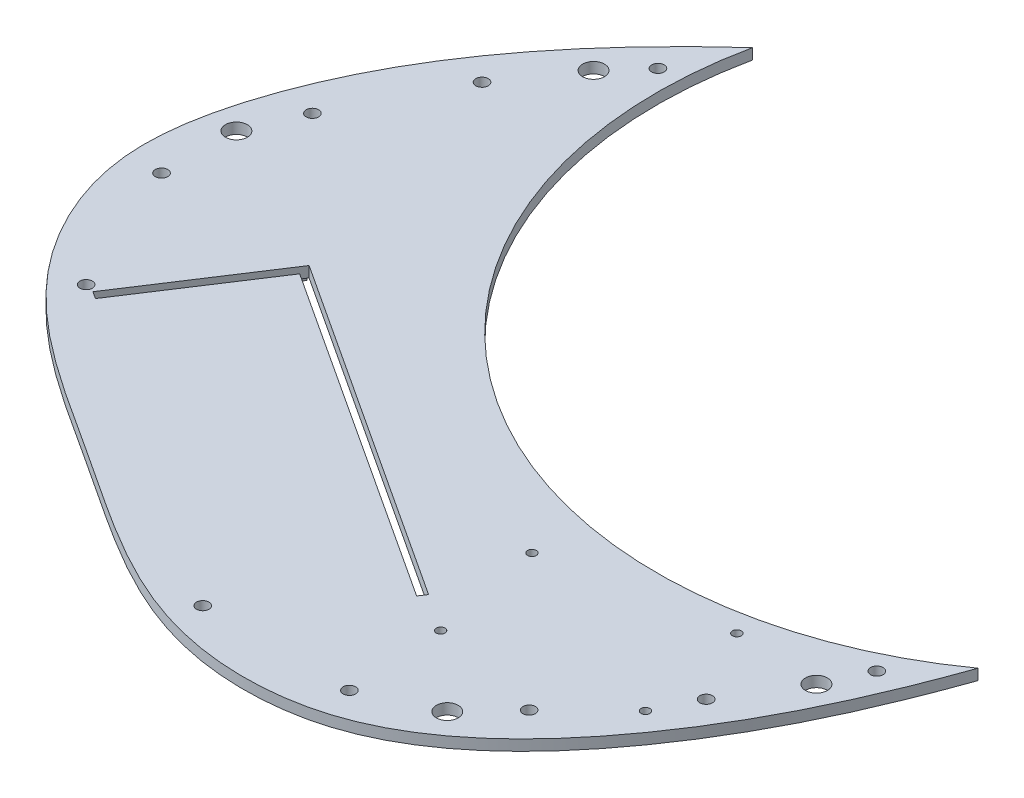
SolidWorks part; units mm, degrees
ref_plane "Front Plane" through (0, 0, 0) normal (0, 0, 1) x (1, 0, 0)
ref_plane "Top Plane" through (0, 0, 0) normal (0, 1, 0) x (1, 0, 0)
ref_plane "Right Plane" through (0, 0, 0) normal (1, 0, 0) x (0, 0, -1)
sketch "Sketch1" plane through (0, 0, 0) normal (0, 1, 0) x (1, 0, 0)
  line L0 (0, 0) -> (0, 58.1546) construction
  circle A0 centre (0, 29.0773) radius 4.9726
extrude "Boss-Extrude1" add sketch "Sketch1" along normal blind 2.5
sketch "Sketch3" plane through (0, 2.5, 0) normal (0, 1, 0) x (1, 0, 0)
  point P0 (0, 29.0773)
sketch "Sketch4" plane through (0, 2.5, 0) normal (0, 1, 0) x (1, 0, 0)
  arc A0 (127.8362, 60.0219) -> (-23.0143, 158.5764) centre (71.5138, 138.5385) cw
  spline S0 degree 3 poles (-23.0143, 158.5764) (-43.5254, 139.9346) (-67.442, 110.6065) (-77.0529, 62.2895) (-62.2823, 29.9156) (-37.7055, 11.9817) (-7.3418, -7.1852) (21.5414, -27.9257) (71.8699, -27.6215) (107.5055, 10.8983) (121.7705, 42.9102) (127.8362, 60.0219) knots 0 0 0 0 0.208615 0.280864 0.361665 0.463001 0.507838 0.636521 0.725182 0.864473 1 1 1 1
  spline S1 degree 3 poles (127.8362, 60.0219) (117.8116, 31.8423) (99.3254, -5.8403) (50.0509, -31.8426) (12.7306, -21.8834) (-18.6736, 0.4949) (-51.7822, 20.2645) (-75.8943, 50.4406) (-71.8759, 106.0099) (-44.7933, 138.0763) (-23.0143, 158.5764) knots 0.001048 0.001048 0.001048 0.001048 0.232378 0.297499 0.407563 0.5 0.592437 0.702501 0.767622 0.998952 0.998952 0.998952 0.998952 construction
extrude "Boss-Extrude2" add sketch "Sketch4" against normal blind 2.5
sketch "Sketch5" plane through (0, 0, 0) normal (0, -1, 0) x (-1, 0, 0)
  line L0 (-100.0794, 11.3416) -> (-94.3668, 41.2815)
  line L1 (-100.0794, 11.3416) -> (-56.4171, 3.0108)
  line L2 (-94.3668, 41.2815) -> (-50.7045, 32.9506)
  line L3 (-56.4171, 3.0108) -> (-50.7045, 32.9506)
  line L4 (-97.2231, 26.3116) -> (-53.5608, 17.9807) construction
  line L5 (-72.5356, 37.1161) -> (-78.2482, 7.1762) construction
  line L6 (-53.5608, 17.9807) -> (-27.1139, 12.9346) construction
  line L7 (-28.3016, 6.7096) -> (-54.7485, 11.7557)
  line L8 (-28.3016, 6.7096) -> (-25.9261, 19.1596)
  line L9 (-54.7485, 11.7557) -> (-52.373, 24.2057)
  line L10 (-25.9261, 19.1596) -> (-52.373, 24.2057)
  line L11 (-28.3016, 6.7096) -> (-52.373, 24.2057) construction
  line L12 (-54.7485, 11.7557) -> (-25.9261, 19.1596) construction
  circle A0 centre (-92.8526, 39.0532) radius 1.016
  circle A1 centre (-97.8511, 12.8558) radius 1.016
  circle A2 centre (-52.9327, 31.4364) radius 1.016
  circle A3 centre (-57.9313, 5.239) radius 1.016
  point P12 (-40.3373, 15.4576)
  point P19 (-40.3373, 15.4576)
  dimension "D3" = 2.032
  dimension "D1" = 30.48
  dimension "D2" = 44.45
  dimension "D4" = 1.905
  dimension "D5" = 1.905
  dimension "D6" = 90
  dimension "D7" = 26.924
  dimension "D8" = 12.6746
extrude "Cut-Extrude1" cut sketch "Sketch5" against normal blind 2.5 contours A1 | A3 | A2 | A0
sketch "Sketch6" plane through (0, 0, 0) normal (0, -1, 0) x (-1, 0, 0)
  line L0 (-18.6634, 57.6441) -> (18.7429, -0.0575) construction
  arc A0 (-127.8362, 60.0219) -> (23.0143, 158.5764) centre (-71.5138, 138.5385) ccw construction
  spline S0 degree 3 poles (23.0143, 158.5764) (43.5254, 139.9346) (67.442, 110.6065) (77.0529, 62.2895) (62.2823, 29.9156) (37.7055, 11.9817) (7.3418, -7.1852) (-21.5414, -27.9257) (-71.8699, -27.6215) (-107.5055, 10.8983) (-121.7705, 42.9102) (-127.8362, 60.0219) knots 0 0 0 0 0.208615 0.280864 0.361665 0.463001 0.507838 0.636521 0.725182 0.864473 1 1 1 1 construction
  point P7 (0.0398, 28.7933)
sketch "Sketch7" plane through (0, 0, 0) normal (0, -1, 0) x (-1, 0, 0)
  line L0 (-71.5138, 138.5385) -> (26.7642, 151.4961) construction
  circle A0 centre (-116.6846, 47.6995) radius 1.45
  circle A1 centre (-102.5377, 22.2427) radius 1.45
  circle A2 centre (-84.1805, -0.4707) radius 1.45
  circle A3 centre (-59.3634, -17.3589) radius 1.45
  circle A4 centre (-25.3354, -17.3589) radius 1.45
  circle A5 centre (-67.32, 301.0773) radius 1.45
  circle A6 centre (-100.1852, 292.2577) radius 1.45
  circle A7 centre (-119.7769, 269.5144) radius 1.45
  circle A8 centre (-131.6199, 242.8193) radius 1.45
  circle A9 centre (-138.6853, 214.5657) radius 1.45
  spline S0 degree 3 poles (26.7642, 151.4961) (30.3096, 147.9997) (33.7564, 144.4255) (37.0762, 140.7515) knots 0 0 0 0 1 1 1 1 construction
  dimension "D1" = 2.9
  dimension "D2" = 2.9
  dimension "D3" = 2.9
  dimension "D4" = 2.9
  dimension "D5" = 2.9
extrude "Cut-Extrude2" cut sketch "Sketch7" against normal blind 22.5
sketch "Sketch8" plane through (0, 0, 0) normal (0, -1, 0) x (1, 0, 0)
  line L0 (29.6633, -46.9072) -> (4.4122, -63.4044)
  line L1 (29.6633, -46.9072) -> (18.3758, -29.6302)
  line L2 (4.4122, -63.4044) -> (-6.8753, -46.1274)
  line L3 (18.3758, -29.6302) -> (-6.8753, -46.1274)
  line L4 (127.8362, -60.0219) -> (-23.0143, -158.5764) construction
  line L5 (52.411, -109.2991) -> (-31.6403, 19.3523) construction
  line L6 (-32.251, -61.1889) -> (-49.5281, -72.4765)
  line L7 (-32.251, -61.1889) -> (-48.7482, -35.9378)
  line L8 (-49.5281, -72.4765) -> (-66.0253, -47.2254)
  line L9 (-48.7482, -35.9378) -> (-66.0253, -47.2254)
  line L10 (18.3758, -29.6302) -> (-124.1115, -122.7207) construction
  line L11 (39.5253, -12.7786) -> (-30.8034, -58.7261) construction
  line L12 (-30.8034, -58.7261) -> (-50.7, -28.2717) construction
  line L13 (-50.7, -28.2717) -> (19.6287, 17.6759) construction
  line L14 (39.5253, -12.7786) -> (19.6287, 17.6759) construction
  line L15 (-40.4996, -48.5634) -> (-57.7767, -59.8509) construction
  line L16 (-31.5563, -62.2521) -> (-48.765, -73.495)
  line L17 (-31.5563, -62.2521) -> (-30.5144, -63.8469)
  line L18 (-48.765, -73.495) -> (-47.7231, -75.0898)
  line L19 (-30.5144, -63.8469) -> (-47.7231, -75.0898)
  line L20 (3.3554, -64.1089) -> (1.7606, -65.1508)
  line L21 (3.3554, -64.1089) -> (-7.9385, -46.822)
  line L22 (1.7606, -65.1508) -> (-9.5333, -47.8639)
  line L23 (-7.9385, -46.822) -> (-9.5333, -47.8639)
  line L24 (30.733, -46.2224) -> (32.3278, -45.1805)
  line L25 (19.439, -28.9355) -> (21.0338, -27.8936)
  line L26 (32.3278, -45.1805) -> (21.0338, -27.8936)
  line L27 (30.733, -46.2224) -> (19.439, -28.9355)
  line L28 (23.1176, -31.0832) -> (-7.4495, -51.0535)
  line L29 (-49.4428, -34.8746) -> (-50.4847, -33.2798)
  line L30 (-66.6514, -46.1174) -> (-67.6934, -44.5226)
  line L31 (-49.4428, -34.8746) -> (-66.6514, -46.1174)
  line L32 (-50.4847, -33.2798) -> (-67.6934, -44.5226)
  line L33 (-33.704, -65.9308) -> (-53.6743, -35.3636)
  line L34 (-63.7958, -41.9763) -> (-62.7539, -43.5711)
  point P10 (17.0378, -55.1558)
  point P23 (-15.5357, -5.2979)
  point P24 (4.361, -35.7523)
  dimension "D1" = 30.1625
  dimension "D2" = 20.6375
  dimension "D3" = 0
  dimension "D4" = 0
  dimension "D5" = 20.6375
  dimension "D6" = 30.1625
  dimension "D7" = 360
  dimension "D8" = 360
  dimension "D9" = 2.54
  dimension "D10" = 2.54
  dimension "D11" = 1.27
  dimension "D12" = 0
  dimension "D13" = 1.905
  dimension "D14" = 0
  dimension "D15" = 1.27
  dimension "D16" = 1.905
  dimension "D17" = 0
  dimension "D18" = 3.81
  dimension "D19" = 3.81
extrude "Boss-Extrude3" add sketch "Sketch8" along normal blind 2.032 contours L26 L28 L27 L24 | L21 L28 L22 L20 | L19 L33 L16 L18 | L32 L34 L31 L33
sketch "Sketch9" plane through (0, -2.032, 0) normal (0, -1, 0) x (-1, 0, 0)
  line L0 (-32.3278, 45.1805) -> (-23.1176, 31.0832)
  line L1 (-32.3278, 45.1805) -> (-29.1382, 47.2644)
  line L2 (-23.1176, 31.0832) -> (-19.928, 33.1671)
  line L3 (-29.1382, 47.2644) -> (-19.928, 33.1671)
  line L4 (-1.7606, 65.1508) -> (7.4495, 51.0535)
  line L5 (-1.7606, 65.1508) -> (-4.9502, 63.067)
  line L6 (7.4495, 51.0535) -> (4.2599, 48.9697)
  line L7 (-4.9502, 63.067) -> (4.2599, 48.9697)
  line L8 (47.7231, 75.0898) -> (33.704, 65.9308)
  line L9 (47.7231, 75.0898) -> (49.8069, 71.9002)
  line L10 (33.704, 65.9308) -> (35.7879, 62.7411)
  line L11 (49.8069, 71.9002) -> (35.7879, 62.7411)
  line L12 (63.7958, 41.9763) -> (53.6743, 35.3636)
  line L13 (63.7958, 41.9763) -> (61.712, 45.1659)
  line L14 (53.6743, 35.3636) -> (51.5905, 38.5532)
  line L15 (61.712, 45.1659) -> (51.5905, 38.5532)
  dimension "D1" = 3.81
  dimension "D2" = 3.81
  dimension "D3" = 3.81
  dimension "D4" = 3.81
extrude "Boss-Extrude4" add sketch "Sketch9" along normal blind 1.27
sketch "Sketch10" plane through (0, 0, 0) normal (0, -1, 0) x (-1, 0, 0)
  line L0 (-18.9829, 24.3534) -> (23.5453, 52.1381)
  line L1 (-18.9829, 24.3534) -> (-0.6449, -3.7152)
  line L2 (23.5453, 52.1381) -> (41.8833, 24.0695)
  line L3 (-0.6449, -3.7152) -> (41.8833, 24.0695)
  line L4 (4.2599, 48.9697) -> (7.4495, 51.0535) construction
  line L5 (-20.7832, 20.1431) -> (-18.6568, 21.5324)
  line L6 (-20.7832, 20.1431) -> (-5.2238, -3.6727)
  line L7 (-18.6568, 21.5324) -> (-3.0974, -2.2834)
  line L8 (-5.2238, -3.6727) -> (-3.0974, -2.2834)
  line L9 (2.2812, 38.2458) -> (20.6192, 10.1772) construction
  line L10 (43.6837, 28.2798) -> (41.5572, 26.8906)
  line L11 (25.9978, 50.7064) -> (41.5572, 26.8906)
  line L12 (28.1242, 52.0956) -> (43.6837, 28.2798)
  line L13 (28.1242, 52.0956) -> (25.9978, 50.7064)
  dimension "D1" = 0
  dimension "D2" = 50.8
  dimension "D3" = 33.528
  dimension "D4" = 0
  dimension "D5" = 2.54
  dimension "D6" = 2.54
  dimension "D7" = 1.27
  dimension "D8" = 2.54
fillet "Fillet1" radius 1.27 4 edges
extrude "Boss-Extrude5" add sketch "Sketch10" along normal blind 6.35 contours L6 L8 L7 L5 | L12 L13 L11 L10
sketch "Sketch11" plane through (0, -6.35, 0) normal (0, -1, 0) x (-1, 0, 0)
  line L0 (-20.7832, 20.1431) -> (-5.2238, -3.6727)
  line L1 (-20.7832, 20.1431) -> (-15.4672, 23.6162)
  line L2 (-5.2238, -3.6727) -> (0.0923, -0.1996)
  line L3 (-15.4672, 23.6162) -> (0.0923, -0.1996)
  line L4 (28.1242, 52.0956) -> (43.6837, 28.2798)
  line L5 (28.1242, 52.0956) -> (22.8082, 48.6225)
  line L6 (43.6837, 28.2798) -> (38.3676, 24.8067)
  line L7 (22.8082, 48.6225) -> (38.3676, 24.8067)
  dimension "D1" = 6.35
  dimension "D2" = 6.35
extrude "Boss-Extrude6" add sketch "Sketch11" along normal blind 2.54
fillet "Fillet2" radius 1.27 2 edges
sketch "Sketch12" plane through (0, 0, 0) normal (0, -1, 0) x (-1, 0, 0)
  line L0 (-127.8362, 60.0219) -> (23.0143, 158.5764) construction
  line L1 (-52.411, 109.2991) -> (47.38, -43.444) construction
  circle A0 centre (-112.3114, 38.0674) radius 2.54
  circle A1 centre (-74.9849, -10.2682) radius 2.54
  circle A2 centre (66.1532, 81.941) radius 2.54
  circle A3 centre (36.8831, 135.54) radius 2.54
extrude "Cut-Extrude3" cut sketch "Sketch12" against normal blind 2.54
sketch "Sketch13" plane through (0, 0, 0) normal (0, -1, 0) x (-1, 0, 0)
  line L0 (-127.8362, 60.0219) -> (23.0143, 158.5764) construction
  line L1 (-52.411, 109.2991) -> (51.9826, -50.4888) construction
ref_plane "Plane1" through (-13.3141, 0, -8.6984) normal (0.8372, 0, 0.5469) x (0.5469, 0, -0.8372)
mirror "Mirror1" about plane through (-13.3141, 0, -8.6984) normal (0.8372, 0, 0.5469) of "Cut-Extrude2"
sketch "Sketch14" plane through (0, 0, 0) normal (0, -1, 0) x (1, 0, 0)
  line L0 (-33.704, -65.9308) -> (-53.6743, -35.3636)
  line L1 (-39.3136, -57.3445) -> (-48.0647, -43.9498)
  line L2 (-39.3136, -57.3445) -> (-60.3425, -71.0833)
  line L3 (-48.0647, -43.9498) -> (-69.0936, -57.6886)
  line L4 (-60.3425, -71.0833) -> (-69.0936, -57.6886)
  line L5 (-39.3136, -57.3445) -> (-48.0647, -43.9498)
  line L6 (-64.7181, -64.3859) -> (-43.6892, -50.6472)
  line L7 (23.1176, -31.0832) -> (-7.4495, -51.0535)
  line L8 (14.5314, -36.6928) -> (1.1367, -45.4439)
  line L9 (14.5314, -36.6928) -> (23.9009, -51.034)
  line L10 (1.1367, -45.4439) -> (10.5062, -59.7851)
  line L11 (23.9009, -51.034) -> (10.5062, -59.7851)
  line L12 (17.2035, -55.4095) -> (7.8341, -41.0684)
  point P4 (-43.6892, -50.6472)
  point P7 (-64.7181, -64.3859)
  point P22 (7.8341, -41.0684)
  dimension "D1" = 16
  dimension "D2" = 0
  dimension "D3" = 16
  dimension "D4" = 0
extrude "Cut-Extrude5" cut sketch "Sketch14" against normal blind 2 contours L12 L11 L9 L7 | L11 L12 L8 L10 | L6 L4 L2 L0 | L4 L6 L5 L3
sketch "Sketch15" plane through (0, 0, 0) normal (0, -1, 0) x (-1, 0, 0)
  line L0 (-23.1176, 31.0832) -> (7.4495, 51.0535) construction
  line L1 (33.704, 65.9308) -> (53.6743, 35.3636) construction
  line L2 (-49.2982, 11.0812) -> (30.6778, 63.3316)
  line L3 (-49.2982, 11.0812) -> (-48.2043, 9.4069)
  line L4 (30.6778, 63.3316) -> (31.7717, 61.6573)
  line L5 (-48.2043, 9.4069) -> (31.7717, 61.6573)
  line L6 (30.6778, 63.3316) -> (29.0035, 62.2377)
  line L7 (30.6778, 63.3316) -> (50.4954, 32.9983)
  line L8 (29.0035, 62.2377) -> (48.8211, 31.9044)
  line L9 (50.4954, 32.9983) -> (48.8211, 31.9044)
  dimension "D1" = 0
  dimension "D2" = 2
  dimension "D3" = 2
extrude "Cut-Extrude6" cut sketch "Sketch15" against normal blind 30.194 contours L8 L2 L3 L5 | L2 L8 L5 L4 | L9 L7 L5 L8
